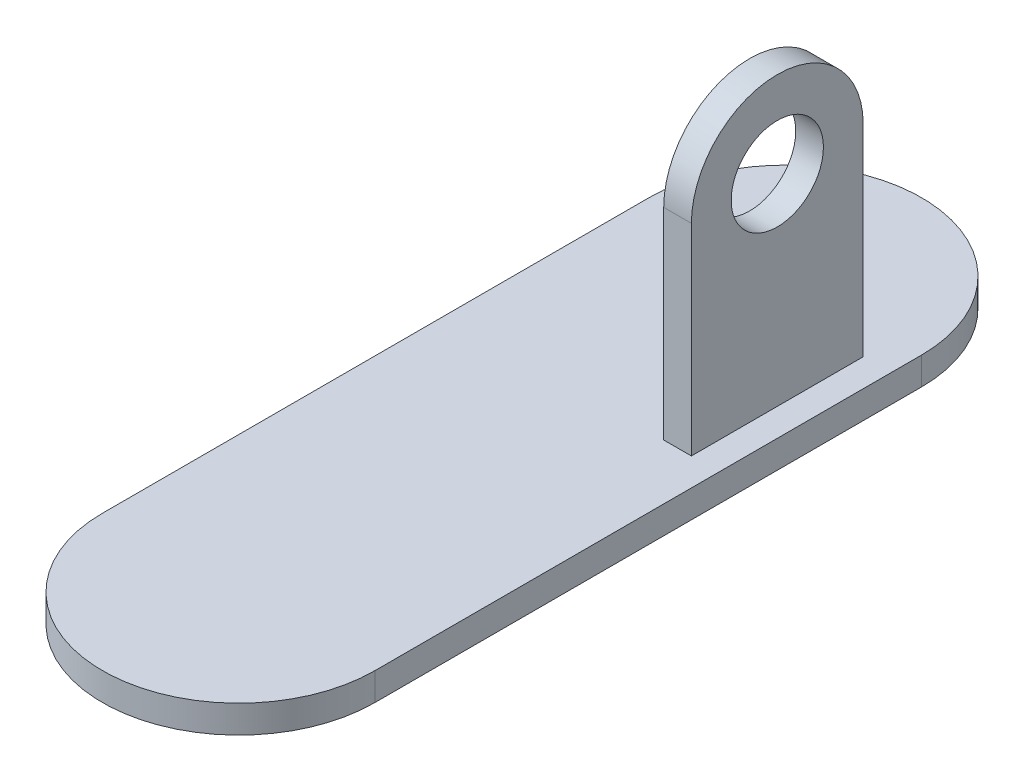
SolidWorks part; units mm, degrees
material "6061 Alloy"
ref_plane "Front Plane" through (0, 0, 0) normal (0, 0, 1) x (1, 0, 0)
ref_plane "Top Plane" through (0, 0, 0) normal (0, 1, 0) x (1, 0, 0)
ref_plane "Right Plane" through (0, 0, 0) normal (1, 0, 0) x (0, 0, -1)
sketch "Sketch1" plane through (0, 0, 0) normal (0, 1, 0) x (1, 0, 0)
  line L0 (0, -88.9) -> (0, 88.9) construction
  line L2 (44.323, 88.9) -> (44.323, -88.9)
  line L3 (0, 0) -> (-26.323, 0) construction
  line L14 (-44.323, 88.9) -> (-44.323, -88.9)
  arc A0 (44.323, 88.9) -> (-44.323, 88.9) centre (0, 88.9) ccw
  arc A1 (-44.323, -88.9) -> (44.323, -88.9) centre (0, -88.9) ccw
  point P8 (0, 0)
  point P13 (-89.4761, 0)
  point P18 (-35.323, 0)
  dimension "D2" = 88.646
  dimension "D1" = 177.8
extrude "Boss-Extrude1" add sketch "Sketch1" along normal blind 9
sketch "Sketch2" plane through (0, 9, 0) normal (0, 1, 0) x (1, 0, 0)
  line L1 (26.323, 78.9) -> (35.323, 78.9)
  line L2 (26.323, 78.9) -> (26.323, 23.02)
  line L3 (26.323, 23.02) -> (35.323, 23.02)
  line L4 (35.323, 78.9) -> (35.323, 23.02)
  line L5 (-44.323, 88.9) -> (44.323, 88.9) construction
  line L6 (44.323, -88.9) -> (44.323, 88.9) construction
  dimension "D1" = 9
  dimension "D2" = 9
  dimension "D3" = 55.88
  dimension "D4" = 10
extrude "Boss-Extrude2" add sketch "Sketch2" along normal blind 65.53
sketch "Sketch3" plane through (35.323, 0, 0) normal (1, 0, 0) x (0, 0, -1)
  line L0 (23.02, 74.53) -> (78.9, 74.53) construction
  circle A0 centre (50.96, 74.53) radius 27.94
extrude "Boss-Extrude3" add sketch "Sketch3" against normal up to surface (9 mm away) up to face at (26.323, 41.765, -50.96)
sketch "Sketch4" plane through (35.323, 0, 0) normal (1, 0, 0) x (0, 0, -1)
  circle A0 centre (50.96, 74.53) radius 15
  dimension "D1" = 30
extrude "Cut-Extrude1" cut sketch "Sketch4" against normal through all
